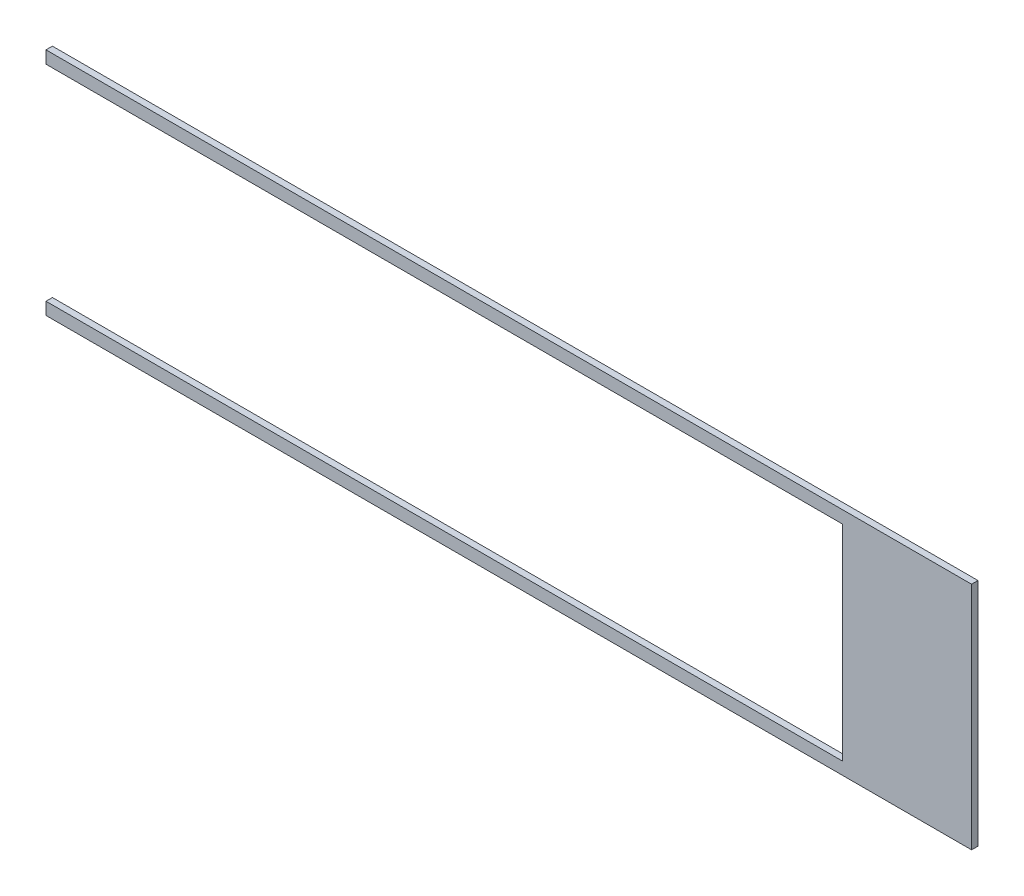
SolidWorks part; units mm, degrees
ref_plane "Front" through (0, 0, 0) normal (0, 0, 1) x (1, 0, 0)
ref_plane "Top" through (0, 0, 0) normal (0, 1, 0) x (1, 0, 0)
ref_plane "Right" through (0, 0, 0) normal (1, 0, 0) x (0, 0, -1)
sketch "Sketch1" plane through (0, 0, 0) normal (0, 0, 1) x (1, 0, 0)
  line L0 (-228.7016, -56.8484) -> (228.7016, -56.8484)
  line L1 (228.7016, -56.8484) -> (228.7016, 56.8484)
  line L2 (228.7016, 56.8484) -> (-228.7016, 56.8484)
  line L3 (-228.7016, 56.8484) -> (-228.7016, 50.6984)
  line L4 (-228.7016, 50.6984) -> (164.9984, 50.6984)
  line L5 (164.9984, 50.6984) -> (164.9984, -50.7492)
  line L6 (164.9984, -50.7492) -> (-228.7016, -50.7492)
  line L7 (-228.7016, -50.7492) -> (-228.7016, -56.8484)
extrude "Boss-Extrude1" add sketch "Sketch1" along normal blind 3.175
